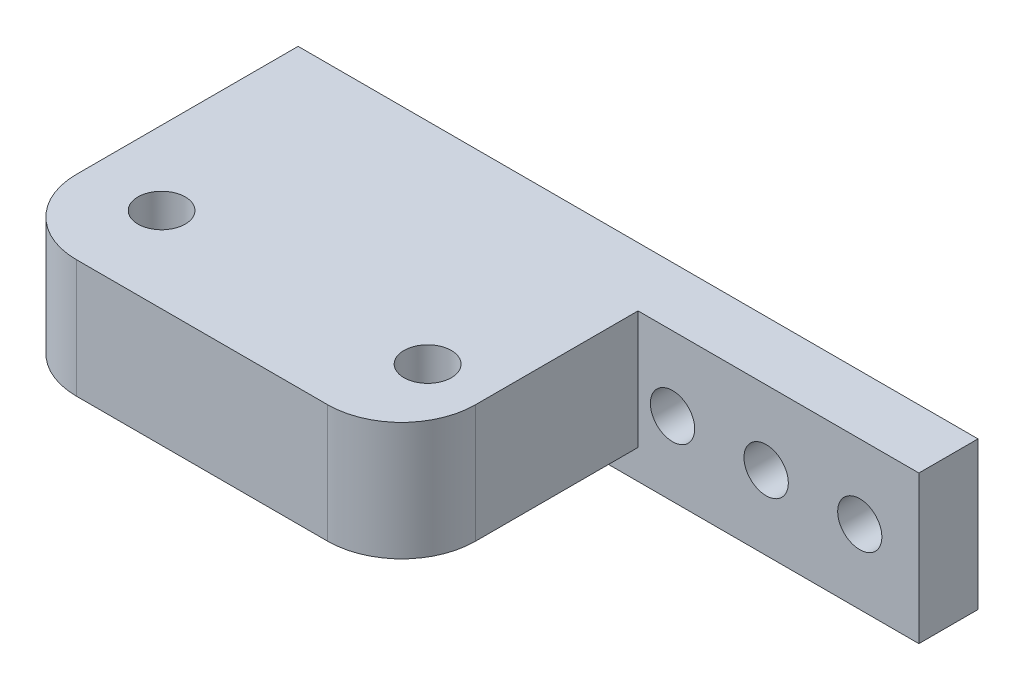
SolidWorks part; units mm, degrees
ref_plane "Front Plane" through (0, 0, 0) normal (0, 0, 1) x (1, 0, 0)
ref_plane "Top Plane" through (0, 0, 0) normal (0, 1, 0) x (1, 0, 0)
ref_plane "Right Plane" through (0, 0, 0) normal (1, 0, 0) x (0, 0, -1)
sketch "Sketch1" plane through (0, 0, 0) normal (0, 0, 1) x (1, 0, 0)
  line L1 (0, 0) -> (46, 0)
  line L2 (0, 0) -> (0, 10)
  line L3 (0, 10) -> (46, 10)
  line L4 (46, 0) -> (46, 10)
  dimension "D1" = 46
  dimension "D2" = 10
extrude "Boss-Extrude1" add sketch "Sketch1" along normal blind 4 contours L2 L3 L4 L1
sketch "Sketch4" plane through (0, 0, 4) normal (0, 0, 1) x (1, 0, 0)
  line L1 (0, 10) -> (27, 10)
  line L2 (0, 10) -> (0, 2)
  line L3 (0, 2) -> (27, 2)
  line L4 (27, 10) -> (27, 2)
  dimension "D1" = 27
  dimension "D2" = 8
extrude "Boss-Extrude2" add sketch "Sketch4" along normal blind 16
sketch "Sketch5" plane through (0, 2, 0) normal (0, -1, 0) x (1, 0, 0)
  circle A0 centre (22.9996, 14.2359) radius 1.601
  circle A1 centre (5.0014, 14.2376) radius 1.5982
extrude "Cut-Extrude2" cut sketch "Sketch5" against normal blind 16
sketch "Sketch6" plane through (0, 0, 0) normal (0, 0, -1) x (-1, 0, 0)
  circle A0 centre (-42, 5) radius 1.4948
  circle A1 centre (-29.3333, 5) radius 1.5
  circle A3 centre (-35.6667, 5) radius 1.5
extrude "Cut-Extrude3" cut sketch "Sketch6" against normal blind 16
fillet "Fillet1" radius 5 2 edges at (27, 6, 20) (0, 6, 20)
